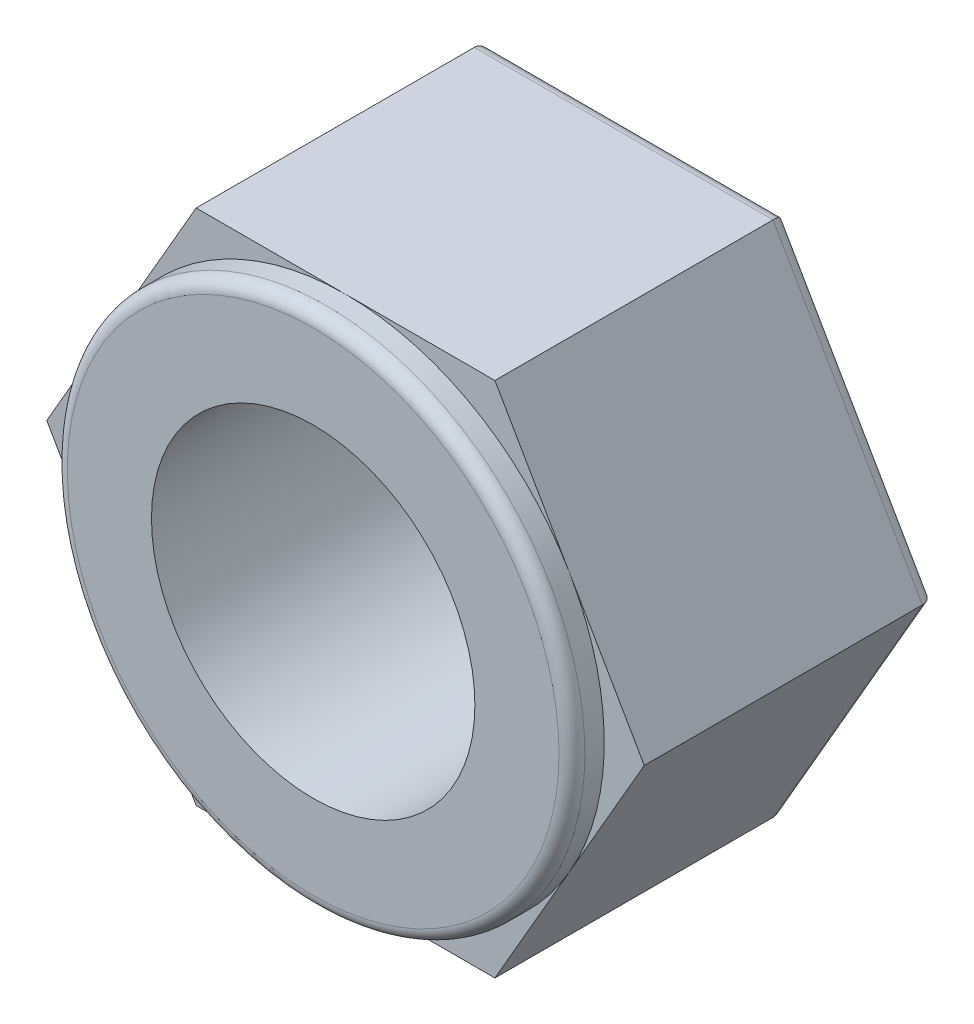
SolidWorks part; units mm, degrees
ref_plane "前视基准面" through (0, 0, 0) normal (0, 0, 1) x (1, 0, 0)
ref_plane "上视基准面" through (0, 0, 0) normal (0, 1, 0) x (1, 0, 0)
ref_plane "右视基准面" through (0, 0, 0) normal (1, 0, 0) x (0, 0, -1)
sketch "草图1" plane through (0, 0, 0) normal (0, 0, 1) x (1, 0, 0)
  line L1 (4.6188, 0) -> (2.3094, 4)
  line L2 (2.3094, 4) -> (-2.3094, 4)
  line L3 (-2.3094, 4) -> (-4.6188, 0)
  line L4 (-4.6188, 0) -> (-2.3094, -4)
  line L5 (-2.3094, -4) -> (2.3094, -4)
  line L6 (2.3094, -4) -> (4.6188, 0)
  circle A0 centre (0, 0) radius 4 construction
  circle A1 centre (0, 0) radius 2.5
  dimension "D2" = 5
  dimension "D1" = 8
extrude "凸台-拉伸1" add sketch "草图1" along normal blind 4.5
sketch "草图2" plane through (0, 0, 4.5) normal (0, 0, 1) x (1, 0, 0)
  circle A0 centre (0, 0) radius 4
  circle A1 centre (0, 0) radius 2.5
extrude "凸台-拉伸2" add sketch "草图2" along normal blind 0.5
fillet "圆角1" radius 0.2 1 edges at (4, 0, 5)
fillet "圆角2" radius 0.2 6 edges at (3.4641, -2, 0) (3.4641, 2, 0) (0, 4, 0) (-3.4641, 2, 0) (-3.4641, -2, 0) (0, -4, 0)
